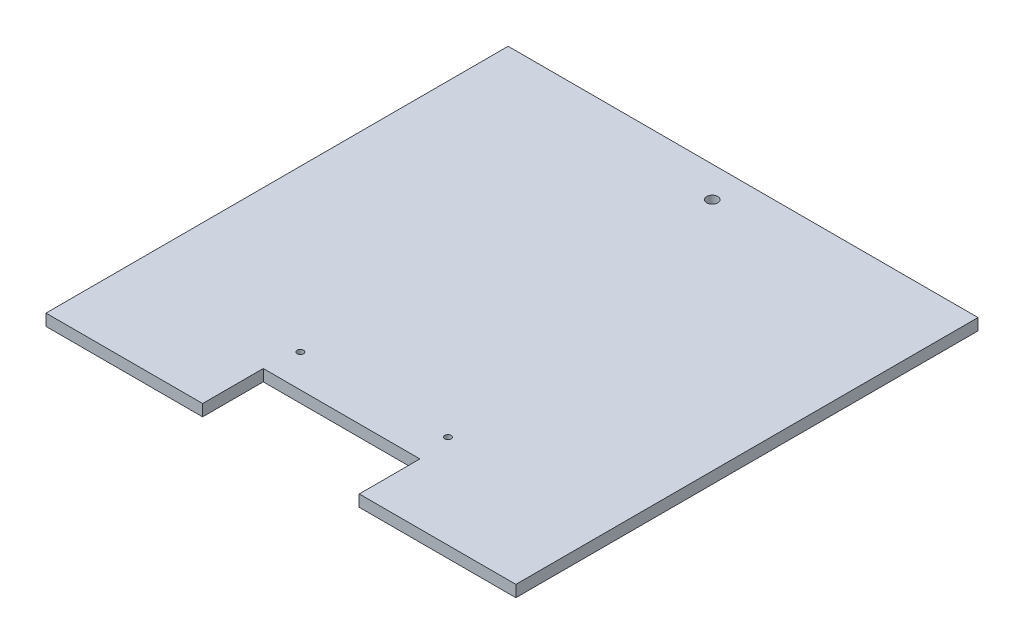
SolidWorks part; units mm, degrees
ref_plane "Front Plane" through (0, 0, 0) normal (0, 0, 1) x (1, 0, 0)
ref_plane "Top Plane" through (0, 0, 0) normal (0, 1, 0) x (1, 0, 0)
ref_plane "Right Plane" through (0, 0, 0) normal (1, 0, 0) x (0, 0, -1)
sketch "Sketch1" plane through (0, 0, 0) normal (0, 1, 0) x (1, 0, 0)
  line L1 (-96.84, -95.25) -> (96.84, -95.25)
  line L2 (-96.84, -95.25) -> (-96.84, 95.25)
  line L3 (-96.84, 95.25) -> (96.84, 95.25)
  line L4 (96.84, -95.25) -> (96.84, 95.25)
  line L5 (-96.84, -95.25) -> (96.84, 95.25) construction
  line L6 (-96.84, 95.25) -> (96.84, -95.25) construction
  point P0 (0, 0)
  dimension "D1" = 193.68
  dimension "D2" = 190.5
extrude "Boss-Extrude1" add sketch "Sketch1" along normal blind 4.78
sketch "Sketch2" plane through (0, 4.78, 0) normal (0, 1, 0) x (1, 0, 0)
  line L0 (96.84, 95.25) -> (-96.84, 95.25) construction
  line L1 (96.84, -95.25) -> (96.84, 95.25) construction
  circle A0 centre (0, 82.55) radius 2.286
  point P4 (0, 95.25)
  dimension "D1" = 4.572
  dimension "D2" = 12.7
  dimension "D3" = 96.84
extrude "Cut-Extrude1" cut sketch "Sketch2" against normal through all
sketch "Sketch3" plane through (0, 4.78, 0) normal (0, 1, 0) x (1, 0, 0)
  line L0 (0, -95.25) -> (-32.28, -95.25)
  line L1 (-96.84, -95.25) -> (96.84, -95.25) construction
  line L2 (-32.28, -95.25) -> (-32.28, -70.25)
  line L3 (-32.28, -70.25) -> (32.28, -70.25)
  line L4 (32.28, -70.25) -> (32.28, -95.25)
  line L5 (32.28, -95.25) -> (0, -95.25)
  line L6 (96.84, -95.25) -> (96.84, 95.25) construction
  dimension "D1" = 64.56
  dimension "D2" = 64.56
  dimension "D3" = 25
extrude "Cut-Extrude2" cut sketch "Sketch3" against normal through all
sketch "Sketch4" plane through (0, 4.78, 0) normal (0, 1, 0) x (1, 0, 0)
  line L5 (32.28, -70.25) -> (-32.28, -70.25) construction
  line L6 (-96.84, 95.25) -> (-96.84, -95.25) construction
  line L16 (35.009, 38.68) -> (35.009, -63.9)
  line L17 (35.009, 38.68) -> (-34.991, 38.68)
  line L18 (-34.991, 38.68) -> (-34.991, -63.9)
  line L19 (35.009, -63.9) -> (-34.991, -63.9)
  line L20 (35.009, 38.68) -> (-34.991, -63.9) construction
  line L21 (-34.991, 38.68) -> (35.009, -63.9) construction
  circle A6 centre (-30.511, -56.7) radius 1.3
  circle A7 centre (30.289, -56.7) radius 1.3
  point P28 (0.009, -12.61)
  dimension "D23" = 2.6
  dimension "D24" = 7.2
  dimension "D25" = 4.48
  dimension "D4" = 60.8
  dimension "D3" = 61.849
  dimension "D1" = 6.35
  dimension "D20" = 102.58
  dimension "D21" = 70
extrude "Cut-Extrude4" cut sketch "Sketch4" against normal through all
